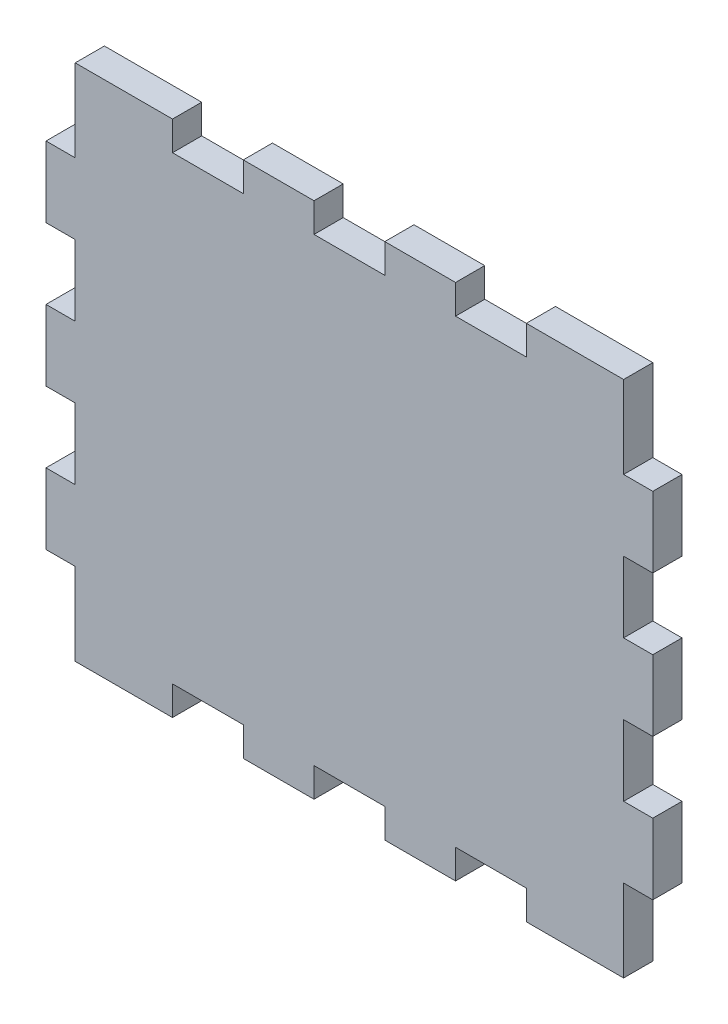
SolidWorks part; units mm, degrees
ref_plane "Plan de face" through (0, 0, 0) normal (0, 0, 1) x (1, 0, 0)
ref_plane "Plan de dessus" through (0, 0, 0) normal (0, 1, 0) x (1, 0, 0)
ref_plane "Plan de droite" through (0, 0, 0) normal (1, 0, 0) x (0, 0, -1)
sketch "Esquisse1" plane through (0, 0, 0) normal (0, 0, 1) x (1, 0, 0)
  line L1 (-31, 26) -> (31, 26)
  line L2 (-31, 26) -> (-31, -26)
  line L3 (-31, -26) -> (31, -26)
  line L4 (31, 26) -> (31, -26)
  line L5 (-31, 26) -> (31, -26) construction
  line L6 (-31, -26) -> (31, 26) construction
  point P0 (0, 0)
  dimension "D1" = 52
  dimension "D2" = 62
extrude "Boss.-Extru.1" add sketch "Esquisse1" along normal blind 3.3
sketch "Esquisse2" plane through (0, 0, 3.3) normal (0, 0, 1) x (1, 0, 0)
  line L0 (-31, -26) -> (31, -26) construction
  line L1 (-4, -26) -> (4, -26) construction
  line L2 (-4, -26) -> (-4, -29.3) construction
  line L3 (-4, -29.3) -> (4, -29.3) construction
  line L4 (4, -26) -> (4, -29.3) construction
  line L6 (4, -26) -> (12, -26)
  line L7 (4, -26) -> (4, -29.3)
  line L8 (4, -29.3) -> (12, -29.3)
  line L9 (12, -26) -> (12, -29.3)
  point P4 (0, -26)
  point P7 (0, -26)
  dimension "D1" = 8
  dimension "D2" = 3.3
extrude "Boss.-Extru.2" add sketch "Esquisse2" against normal blind 3.3
pattern_linear "Répétition linéaire1" count 2 spacing 16 along (1, 0, 0) count 3 spacing 16 along (-1, 0, 0) of "Boss.-Extru.2"
mirror "Symétrie1" about plane through (0, 0, 0) normal (0, 1, 0) of "Répétition linéaire1", "Boss.-Extru.2"
sketch "Esquisse3" plane through (0, 0, 3.3) normal (0, 0, 1) x (1, 0, 0)
  line L1 (-31, 26) -> (-28, 26)
  line L2 (-31, 26) -> (-31, 29.3)
  line L3 (-31, 29.3) -> (-28, 29.3)
  line L4 (-28, 26) -> (-28, 29.3)
  line L5 (28, 29.3) -> (31, 29.3)
  line L6 (28, 29.3) -> (28, 26)
  line L7 (28, 26) -> (31, 26)
  line L8 (31, 29.3) -> (31, 26)
extrude "Boss.-Extru.3" add sketch "Esquisse3" against normal blind 3.3
mirror "Symétrie2" about plane through (0, 0, 0) normal (0, 1, 0) of "Boss.-Extru.3"
sketch "Esquisse4" plane through (0, 0, 3.3) normal (0, 0, 1) x (1, 0, 0)
  line L0 (-31, 29.3) -> (-31, -29.3) construction
  line L1 (-34.3, -4) -> (-31, -4)
  line L2 (-34.3, -4) -> (-34.3, 4)
  line L3 (-34.3, 4) -> (-31, 4)
  line L4 (-31, -4) -> (-31, 4)
  point P4 (-31, 0)
  point P7 (-31, 0)
  dimension "D1" = 8
  dimension "D2" = 3.3
extrude "Boss.-Extru.4" add sketch "Esquisse4" against normal blind 3.3
pattern_linear "Répétition linéaire2" count 2 spacing 16 along (0, 1, 0) count 2 spacing 16 along (0, -1, 0) of "Boss.-Extru.4"
mirror "Symétrie3" about plane through (0, 0, 0) normal (1, 0, 0) of "Répétition linéaire2", "Boss.-Extru.4"
